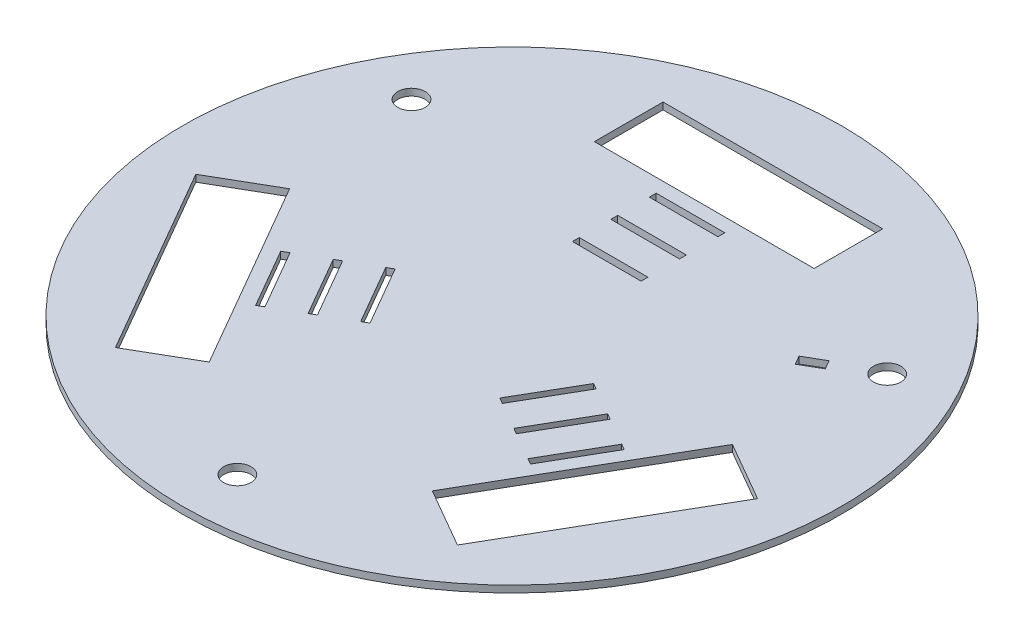
SolidWorks part; units mm, degrees
ref_plane "Front Plane" through (0, 0, 0) normal (0, 0, 1) x (1, 0, 0)
ref_plane "Top Plane" through (0, 0, 0) normal (0, 1, 0) x (1, 0, 0)
ref_plane "Right Plane" through (0, 0, 0) normal (1, 0, 0) x (0, 0, -1)
sketch "Sketch1" plane through (0, 0, 0) normal (0, 1, 0) x (1, 0, 0)
  line L0 (152.4, 304.8) -> (152.4, 0) construction
  line L1 (0, 0) -> (304.8, 0) construction
  line L2 (0, 0) -> (0, 304.8) construction
  line L3 (0, 304.8) -> (304.8, 304.8) construction
  line L4 (304.8, 0) -> (304.8, 304.8) construction
  line L5 (0, 152.4) -> (304.8, 152.4) construction
  circle A0 centre (152.4, 152.4) radius 152.4
  dimension "D1" = 304.8
  dimension "D2" = 304.8
extrude "Boss-Extrude1" add sketch "Sketch1" along normal blind 3.175
sketch "Sketch2" plane through (0, 3.175, 0) normal (0, 1, 0) x (1, 0, 0)
  line L0 (152.4, 152.4) -> (229.3897, 107.95) construction
  line L1 (152.4, 241.3) -> (75.4103, 196.85) construction
  line L2 (75.4103, 196.85) -> (75.4103, 107.95) construction
  line L3 (75.4103, 107.95) -> (152.4, 63.5) construction
  line L4 (152.4, 63.5) -> (229.3897, 107.95) construction
  line L5 (229.3897, 107.95) -> (229.3897, 196.85) construction
  line L6 (229.3897, 196.85) -> (152.4, 241.3) construction
  line L7 (229.3897, 107.95) -> (284.3823, 76.2) construction
  line L8 (152.4, 152.4) -> (75.4103, 107.95) construction
  line L9 (152.4, 152.4) -> (152.4, 304.8) construction
  line L10 (304.8, 304.8) -> (0, 304.8) construction
  line L11 (75.4103, 107.95) -> (20.4177, 76.2) construction
  line L12 (152.4, 152.4) -> (152.4, 63.5) construction
  line L13 (152.4, 63.5) -> (152.4, 0) construction
  line L14 (152.4, 152.4) -> (229.3897, 196.85) construction
  line L15 (229.3897, 196.85) -> (284.3823, 228.6) construction
  line L16 (152.4, 152.4) -> (75.4103, 196.85) construction
  line L17 (75.4103, 196.85) -> (20.4177, 228.6) construction
  line L18 (282.286, 136.0691) -> (231.486, 48.0809)
  line L19 (282.286, 136.0691) -> (254.7897, 151.9441)
  line L20 (254.7897, 151.9441) -> (203.9897, 63.9559)
  line L21 (231.486, 48.0809) -> (203.9897, 63.9559)
  line L22 (231.8279, 124.8732) -> (215.9529, 97.3768)
  line L23 (231.8279, 124.8732) -> (229.0783, 126.4607)
  line L24 (229.0783, 126.4607) -> (213.2033, 98.9643)
  line L25 (215.9529, 97.3768) -> (213.2033, 98.9643)
  line L26 (216.43, 133.7632) -> (200.555, 106.2668)
  line L27 (216.43, 133.7632) -> (213.6803, 135.3507)
  line L28 (213.6803, 135.3507) -> (197.8053, 107.8543)
  line L29 (200.555, 106.2668) -> (197.8053, 107.8543)
  line L30 (229.3897, 107.95) -> (223.8904, 111.125) construction
  line L31 (223.8904, 111.125) -> (208.4925, 120.015) construction
  line L32 (73.314, 48.0809) -> (22.514, 136.0691)
  line L33 (73.314, 48.0809) -> (100.8103, 63.9559)
  line L34 (101.6, 273.05) -> (203.2, 273.05)
  line L35 (101.6, 273.05) -> (101.6, 241.3)
  line L36 (101.6, 241.3) -> (203.2, 241.3)
  line L37 (203.2, 273.05) -> (203.2, 241.3)
  line L38 (100.8103, 63.9559) -> (50.0103, 151.9441)
  line L39 (22.514, 136.0691) -> (50.0103, 151.9441)
  line L40 (88.8471, 97.3768) -> (72.9721, 124.8732)
  line L41 (88.8471, 97.3768) -> (91.5967, 98.9643)
  line L42 (91.5967, 98.9643) -> (75.7217, 126.4607)
  line L43 (72.9721, 124.8732) -> (75.7217, 126.4607)
  line L44 (104.245, 106.2668) -> (88.37, 133.7632)
  line L45 (104.245, 106.2668) -> (106.9947, 107.8543)
  line L46 (136.525, 234.95) -> (168.275, 234.95)
  line L47 (136.525, 234.95) -> (136.525, 231.775)
  line L48 (136.525, 231.775) -> (168.275, 231.775)
  line L49 (168.275, 234.95) -> (168.275, 231.775)
  line L50 (136.525, 217.17) -> (168.275, 217.17)
  line L51 (136.525, 217.17) -> (136.525, 213.995)
  line L52 (136.525, 213.995) -> (168.275, 213.995)
  line L53 (168.275, 217.17) -> (168.275, 213.995)
  line L54 (106.9947, 107.8543) -> (91.1197, 135.3507)
  line L55 (88.37, 133.7632) -> (91.1197, 135.3507)
  line L56 (119.643, 115.1568) -> (103.768, 142.6532)
  line L57 (80.9096, 111.125) -> (96.3075, 120.015) construction
  line L58 (243.597, 207.8022) -> (245.9782, 203.6778)
  line L59 (243.597, 207.8022) -> (234.7981, 202.7222)
  line L60 (234.7981, 202.7222) -> (237.1794, 198.5978)
  line L61 (245.9782, 203.6778) -> (237.1794, 198.5978)
  line L62 (243.597, 207.8022) -> (237.1794, 198.5978) construction
  line L63 (234.7981, 202.7222) -> (245.9782, 203.6778) construction
  line L64 (119.643, 115.1568) -> (122.3926, 116.7443)
  line L65 (122.3926, 116.7443) -> (106.5176, 144.2407)
  line L66 (103.768, 142.6532) -> (106.5176, 144.2407)
  line L67 (201.032, 142.6532) -> (185.157, 115.1568)
  line L68 (201.032, 142.6532) -> (198.2824, 144.2407)
  line L69 (198.2824, 144.2407) -> (182.4074, 116.7443)
  line L70 (185.157, 115.1568) -> (182.4074, 116.7443)
  line L71 (136.525, 199.39) -> (168.275, 199.39)
  line L72 (136.525, 199.39) -> (136.525, 196.215)
  line L73 (136.525, 196.215) -> (168.275, 196.215)
  line L74 (168.275, 199.39) -> (168.275, 196.215)
  circle A0 centre (152.4, 152.4) radius 76.9897 construction
  circle A1 centre (152.4, 152.4) radius 152.4 construction
  circle A2 centre (152.4, 25.4) radius 6.35
  circle A6 centre (42.4148, 215.9) radius 6.35
  circle A7 centre (262.3852, 215.9) radius 6.35
  point P5 (75.4103, 107.95)
  point P21 (240.3882, 203.2)
  point P24 (152.4, 273.05)
  point P63 (111.7055, 128.905)
  point P76 (152.4, 199.39)
  point P77 (199.6572, 143.4469)
  point P78 (152.4, 234.95)
  dimension "D12" = 6.35
  dimension "D11" = 3.175
  dimension "D15" = 3.175
  dimension "D17" = 31.75
  dimension "D18" = 17.78
  dimension "D19" = 6.35
  dimension "D20" = 101.6
  dimension "D22" = 127
  dimension "D23" = 127
  dimension "D24" = 127
  dimension "D25" = 12.7
  dimension "D26" = 12.7
  dimension "D48" = 12.7
  dimension "D3" = 31.75
  dimension "D4" = 3.175
  dimension "D5" = 3.175
  dimension "D6" = 31.75
  dimension "D7" = 17.78
  dimension "D8" = 6.35
  dimension "D9" = 101.6
  dimension "D10" = 31.75
  dimension "D13" = 101.6
  dimension "D14" = 31.75
  dimension "D16" = 3.175
  dimension "D21" = 31.75
  dimension "D27" = 152.4
  dimension "D28" = 88.9
  dimension "D29" = 88.9
  dimension "D30" = 3.175
  dimension "D31" = 61.595
  dimension "D32" = 61.595
  dimension "D33" = 31.75
  dimension "D34" = 4.7625
  dimension "D35" = 17.78
  dimension "D36" = 10.16
  dimension "D37" = 101.6
  dimension "D38" = 31.75
  dimension "D39" = 3.175
  dimension "D40" = 17.78
  dimension "D41" = 17.78
  dimension "D42" = 3.175
  dimension "D43" = 31.75
  dimension "D44" = 31.75
  dimension "D45" = 3.175
  dimension "D46" = 17.78
  dimension "D47" = 34.925
extrude "Cut-Extrude1" cut sketch "Sketch2" against normal blind 3.175
